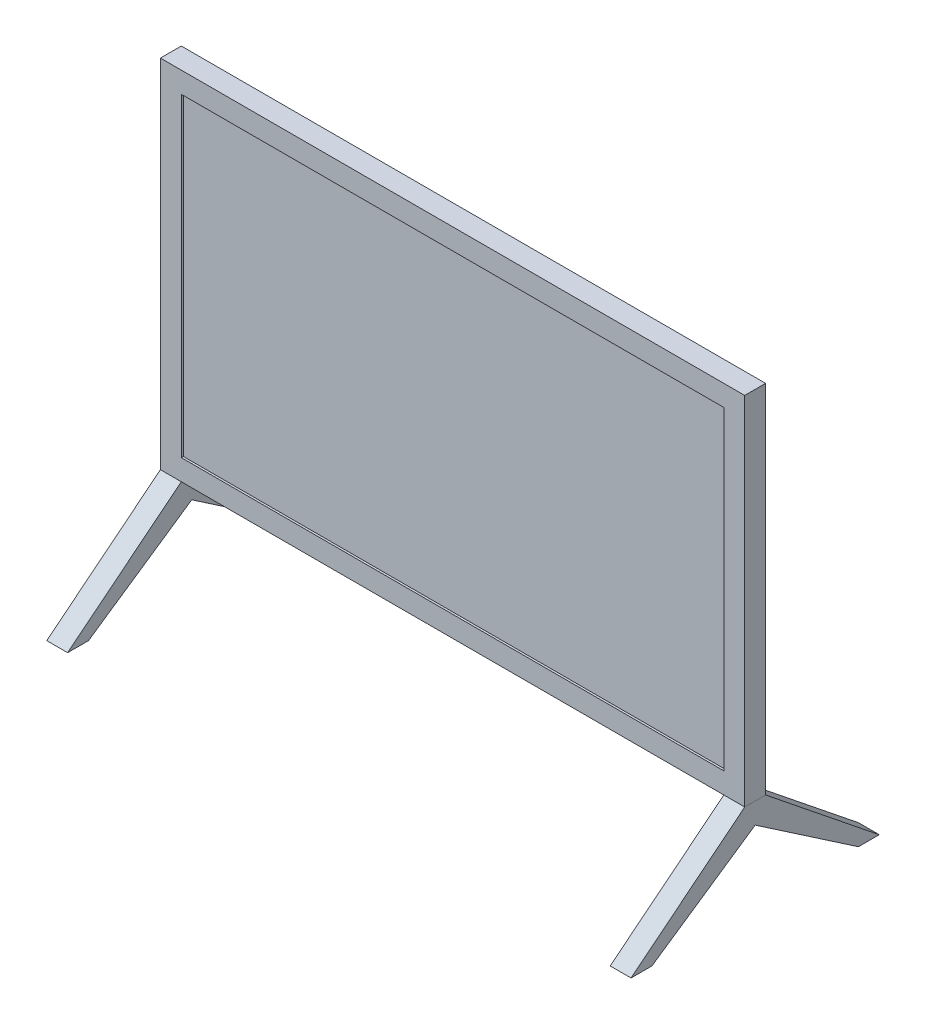
SolidWorks part; units mm, degrees
ref_plane "Plan de face" through (0, 0, 0) normal (0, 0, 1) x (1, 0, 0)
ref_plane "Plan de dessus" through (0, 0, 0) normal (0, 1, 0) x (1, 0, 0)
ref_plane "Plan de droite" through (0, 0, 0) normal (1, 0, 0) x (0, 0, -1)
sketch "Esquisse1" plane through (0, 0, 0) normal (0, 0, 1) x (1, 0, 0)
  line L0 (-263.7, 305.9139) -> (-263.7, 0) construction
  line L1 (0, 0) -> (-527.4, 0)
  line L2 (0, 0) -> (0, 305.9139)
  line L3 (0, 305.9139) -> (-527.4, 305.9139)
  line L4 (-527.4, 0) -> (-527.4, 305.9139)
  line L6 (20.3, -20.3) -> (-547.7, -20.3)
  line L7 (20.3, -20.3) -> (20.3, 326.2139)
  line L8 (20.3, 326.2139) -> (-547.7, 326.2139)
  line L9 (-547.7, -20.3) -> (-547.7, 326.2139)
  line L10 (20.3, -20.3) -> (-547.7, 326.2139) construction
  line L11 (20.3, 326.2139) -> (-547.7, -20.3) construction
  point P7 (-263.7, 152.957)
  dimension "D1" = 527.4
  dimension "D2" = 609.7
  dimension "D3" = 305.9139
  dimension "D4" = 20.3
  dimension "D5" = 20.3
extrude "Boss.-Extru.1" add sketch "Esquisse1" along normal blind 20.3
sketch "Esquisse2" plane through (0, 0, 0) normal (0, 1, 0) x (1, 0, 0)
  line L0 (-527.4, -20.3) -> (-527.4, 0) construction
  line L1 (-527.4, -18.3) -> (0, -18.3)
  line L2 (-527.4, -18.3) -> (-527.4, 0)
  line L3 (-527.4, 0) -> (0, 0)
  line L4 (0, -18.3) -> (0, 0)
  line L5 (0, -20.3) -> (0, 0) construction
  line L6 (-527.4, 0) -> (0, 0) construction
  line L7 (-527.4, -20.3) -> (0, -20.3) construction
  dimension "D1" = 0
  dimension "D2" = 2
extrude "Boss.-Extru.2" add sketch "Esquisse2" along normal up to next
sketch "Esquisse3" plane through (-547.7, 0, 0) normal (-1, 0, 0) x (0, 0, 1)
  line L0 (10.15, 326.2139) -> (10.15, -108.9861) construction
  line L1 (20.3, 326.2139) -> (0, 326.2139) construction
  line L2 (10.15, -20.3) -> (10.15, -40.6)
  line L3 (-111.9255, -108.9861) -> (164.4037, -108.9861) construction
  line L4 (20.3, -20.3) -> (0, -20.3) construction
  line L6 (10.15, -40.6) -> (-90.1867, -108.9861)
  line L7 (-90.1867, -108.9861) -> (-110.4867, -108.9861)
  line L8 (0, -20.3) -> (-110.4867, -108.9861)
  line L9 (0, -20.3) -> (20.3, -20.3)
  line L10 (20.3, -20.3) -> (130.7867, -108.9861)
  line L11 (110.4867, -108.9861) -> (130.7867, -108.9861)
  line L12 (10.15, -40.6) -> (110.4867, -108.9861)
  line M11 (0, -20.3) -> (20.3, -20.3)
  dimension "D1" = 20.3
  dimension "D2" = 20.3
extrude "Boss.-Extru.3" add sketch "Esquisse3" against normal blind 20.3 separate body contours L8 L7 L6 L2 M11 | L2 L12 L11 L10 M11
ref_plane "Plan1" through (-263.7, 0, 0) normal (-1, 0, 0) x (0, 0, 1)
mirror "Symétrie2" about plane through (-263.7, 0, 0) normal (-1, 0, 0) of bodies 103
